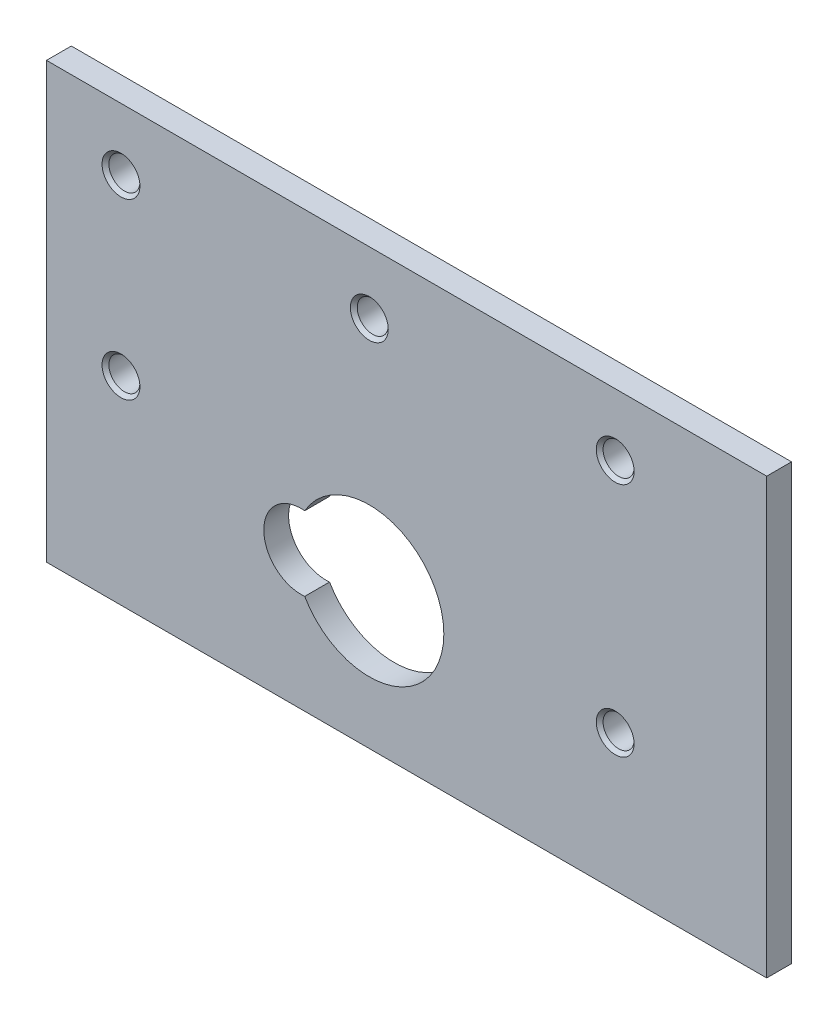
SolidWorks part; units mm, degrees
ref_plane "Front Plane" through (0, 0, 0) normal (0, 0, 1) x (1, 0, 0)
ref_plane "Top Plane" through (0, 0, 0) normal (0, 1, 0) x (1, 0, 0)
ref_plane "Right Plane" through (0, 0, 0) normal (1, 0, 0) x (0, 0, -1)
sketch "Sketch1" plane through (0, 0, 0) normal (0, 0, 1) x (1, 0, 0)
  line L1 (-29, 17.5) -> (29, 17.5)
  line L2 (-29, 17.5) -> (-29, -17.5)
  line L3 (-29, -17.5) -> (29, -17.5)
  line L4 (29, 17.5) -> (29, -17.5)
  line L5 (-29, 17.5) -> (29, -17.5) construction
  line L6 (-29, -17.5) -> (29, 17.5) construction
  point P0 (0, 0)
  dimension "D1" = 58
  dimension "D2" = 35
extrude "Boss-Extrude2" add sketch "Sketch1" along normal blind 2
hole_wizard "M3x0.5 Tapped Hole3" positions "Sketch10" profile "Sketch9" tap size "M3x0.5" standard "JIS" end condition through all
sketch "Sketch10" plane through (0, 0, 2) normal (0, 0, 1) x (1, 0, 0)
  line L0 (-29, -17.5) -> (29, -17.5) construction
  line L1 (29, -17.5) -> (29, 17.5) construction
  point P0 (-23, 12.5)
  point P2 (-3, 12.5)
  point P4 (16.8, 12.5)
  point P6 (16.8, -6.5)
  point P8 (-23, -1.5)
  point P16 (-0.691, 11.7166)
  point P17 (0, 0)
  point P18 (0, 0)
  point P19 (0, 0)
  point P22 (0, 0)
  point P23 (0, 0)
  point P24 (0, 0)
  point P25 (0, 0)
  dimension "D1" = 16
  dimension "D2" = 20
  dimension "D3" = 19.8
  dimension "D4" = 12.2
  dimension "D5" = 19
  dimension "D6" = 11
sketch "Sketch9" plane through (-23, 12.5, 2) normal (1, 0, 0) x (0, -1, 0)
  line L0 (0, 0) -> (0, 2)
  line L1 (0, 2) -> (1.25, 2)
  line L2 (1.25, 2) -> (1.25, 0.275)
  line L3 (1.25, 0.275) -> (1.525, 0)
  line L5 (1.525, 0) -> (0, 0)
  line L6 (-1.25, 0.275) -> (-1.525, 0) construction
  line L11 (0, -6.35) -> (0, 107.95) construction
  dimension "Thru Tap Drill Dia." = 2.5
  dimension "Thru Tap Drill Depth" = 2
  dimension "Near C'Sink Dia." = 3.05
  dimension "Near C'Sink Angle" = 90
cosmetic thread "Hole Thread11" parameters "D2"=3
cosmetic thread "Hole Thread12" parameters "D2"=3
cosmetic thread "Hole Thread13" parameters "D2"=3
cosmetic thread "Hole Thread14" parameters "D2"=3
cosmetic thread "Hole Thread15" parameters "D2"=3
sketch "Sketch11" plane through (0, 0, 2) normal (0, 0, 1) x (1, 0, 0)
  line L0 (-29, -17.5) -> (29, -17.5) construction
  line L1 (-29, 17.5) -> (-29, -17.5) construction
  arc A0 (-8.2045, -3.5146) -> (-8.2045, -9.4854) centre (-8.5, -6.5) ccw
  arc A1 (-8.2045, -9.4854) -> (-8.2045, -3.5146) centre (-3, -6.5) ccw
  point P5 (-9, -6.5)
  dimension "D2" = 12
  dimension "D3" = 6
  dimension "D4" = 11
  dimension "D1" = 0.5
  dimension "D5" = 26
extrude "Cut-Extrude1" cut sketch "Sketch11" against normal through all
